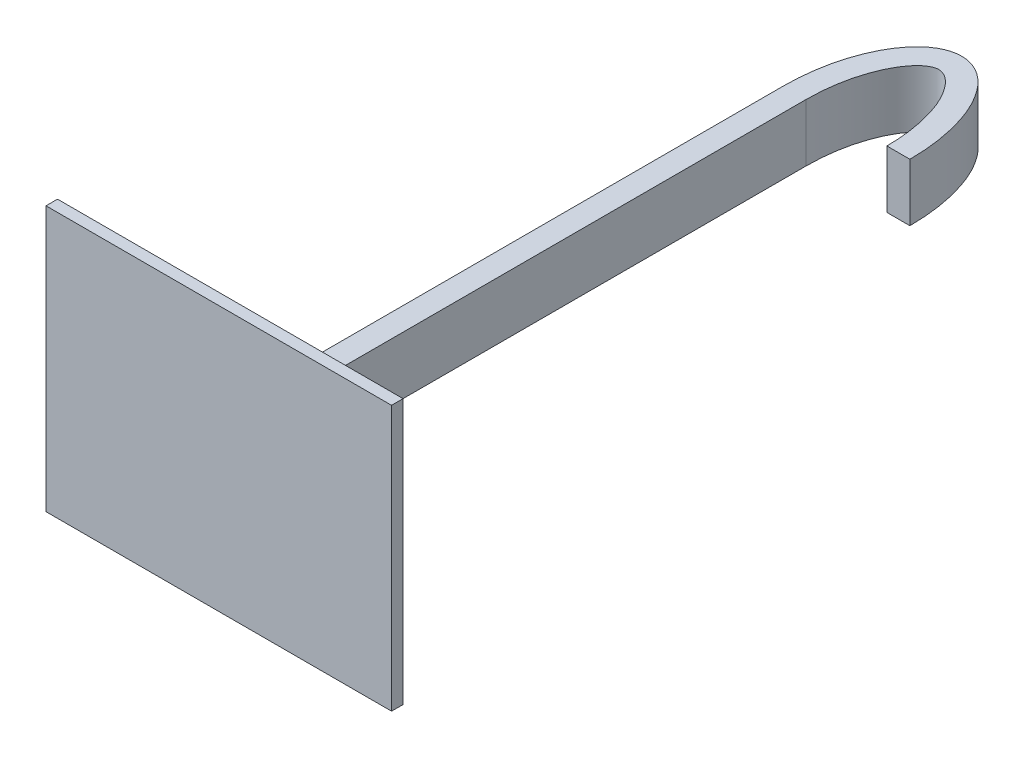
SolidWorks part; units mm, degrees
ref_plane "前视基准面" through (0, 0, 0) normal (0, 0, 1) x (1, 0, 0)
ref_plane "上视基准面" through (0, 0, 0) normal (0, 1, 0) x (1, 0, 0)
ref_plane "右视基准面" through (0, 0, 0) normal (1, 0, 0) x (0, 0, -1)
other "Configuration Table"
sketch "草图1" plane through (0, 0, 0) normal (0, 0, 1) x (1, 0, 0)
  line L1 (15, -11.5) -> (-15, -11.5)
  line L2 (15, -11.5) -> (15, 11.5)
  line L3 (15, 11.5) -> (-15, 11.5)
  line L4 (-15, -11.5) -> (-15, 11.5)
  line L5 (15, -11.5) -> (-15, 11.5) construction
  line L6 (15, 11.5) -> (-15, -11.5) construction
  point P0 (0, 0)
  dimension "D1" = 30
  dimension "D2" = 23
extrude "凸台-拉伸1" add sketch "草图1" along normal blind 1 contours L2 L1 L4 L3
sketch "草图2" plane through (0, 0, 1) normal (0, 0, 1) x (1, 0, 0)
  line L1 (1, -2.5) -> (-1, -2.5)
  line L2 (1, -2.5) -> (1, 2.5)
  line L3 (1, 2.5) -> (-1, 2.5)
  line L4 (-1, -2.5) -> (-1, 2.5)
  line L5 (1, -2.5) -> (-1, 2.5) construction
  line L6 (1, 2.5) -> (-1, -2.5) construction
  point P0 (0, 0)
  dimension "D1" = 5
  dimension "D2" = 2
extrude "凸台-拉伸2" add sketch "草图2" against normal blind 50 contours L2 L1 L4 L3
sketch "草图3" plane through (0, -2.5, 0) normal (0, -1, 0) x (1, 0, 0)
  line L0 (-37.1561, -49) -> (-32.1561, -49) construction
  line L1 (18.0759, -49) -> (10, -49)
  line L2 (4.5, -48.1589) -> (4.5, -46.5797) construction
  line L3 (8, -49) -> (10, -49)
  line L4 (18.0759, -47) -> (7.8747, -47) construction
  line L5 (1, -49) -> (-1, -49)
  arc A0 (-1, -49) -> (10, -49) centre (4.5, -43.1905) ccw construction
  ellipse E0 centre (4.5, -49) end of major axis (4.5, -39) minor radius 5.5 (-1, -49) -> (10, -49) ccw
  spline S0 degree 1 poles (1, -49) (7.8747, -47) knots 0 0 1 1 construction
  spline S1 degree 3 poles (1, -49) (1, -49.6199) (1.0731, -50.8758) (1.4969, -53.2329) (2.2985, -55.1774) (3.2251, -56.3664) (3.8633, -56.8542) (4.3337, -57.0104) (4.6969, -57.0059) (5.1817, -56.8293) (6.0469, -56.1396) (7.2265, -54.2468) (7.8656, -51.5495) (8.0027, -49.5774) (8.0025, -48.3233) (7.9378, -47.4967) (7.8747, -47) knots -1.570796 -1.570796 -1.570796 -1.570796 -1.360248 -1.1497 -0.728605 -0.518057 -0.307509 -0.096961 0.113587 0.324135 0.534683 0.955779 1.376874 1.514003 1.62759 1.79797 1.79797 1.79797 1.79797 only from (1, -49) to (8, -49)
  point P5 (4.5, -49)
  point P17 (4.5, -59)
  dimension "D1" = 8
  dimension "D2" = 10
  dimension "D4" = 11
  dimension "D3" = 2
extrude "凸台-拉伸3" add sketch "草图3" against normal blind 5 contours L3 S1 L5 E0
sketch "草图4" plane through (0, 0, 1) normal (0, 0, 1) x (1, 0, 0)
  line L1 (11.5, -9.5) -> (-11.5, -9.5)
  line L2 (11.5, -9.5) -> (11.5, 9.5)
  line L3 (11.5, 9.5) -> (-11.5, 9.5)
  line L4 (-11.5, -9.5) -> (-11.5, 9.5)
  line L5 (11.5, -9.5) -> (-11.5, 9.5) construction
  line L6 (11.5, 9.5) -> (-11.5, -9.5) construction
  circle A0 centre (-11.5, 9.5) radius 1.5
  circle A1 centre (11.5, 9.5) radius 1.5
  circle A2 centre (11.5, -9.5) radius 1.5
  circle A3 centre (-11.5, -9.5) radius 1.5
  point P0 (0, 0)
  dimension "D3" = 3
  dimension "D4" = 3
  dimension "D5" = 3
  dimension "D6" = 3
  dimension "D1" = 23
  dimension "D2" = 19
